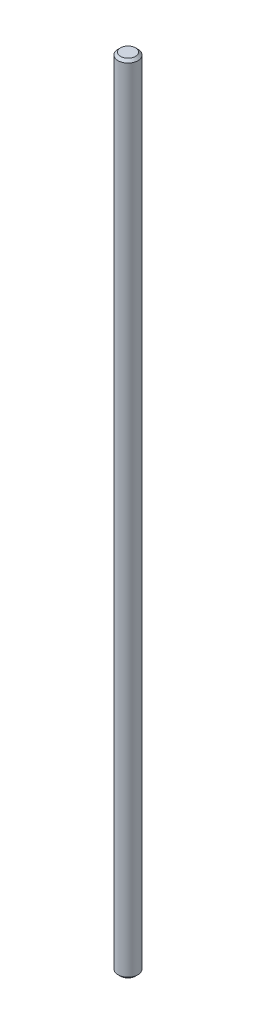
SolidWorks part; units mm, degrees
ref_plane "Front Plane" through (0, 0, 0) normal (0, 0, 1) x (1, 0, 0)
ref_plane "Top Plane" through (0, 0, 0) normal (0, 1, 0) x (1, 0, 0)
ref_plane "Right Plane" through (0, 0, 0) normal (1, 0, 0) x (0, 0, -1)
sketch "Sketch1" plane through (0, 0, 0) normal (0, 1, 0) x (1, 0, 0)
  circle A0 centre (0, 0) radius 2
  dimension "D1" = 4
extrude "Boss-Extrude1" add sketch "Sketch1" along normal blind 160
chamfer "Chamfer1" distance 0.5 angle 45 2 edges at (0, 0, 2) (0, 160, 2)
